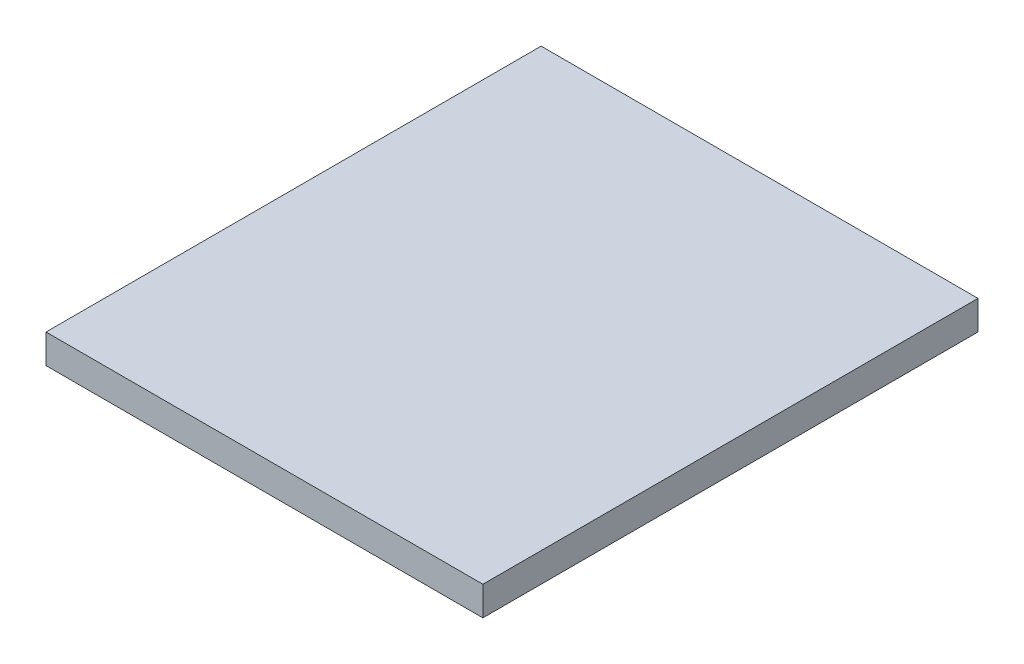
SolidWorks part; units mm, degrees
ref_plane "Alzado" through (0, 0, 0) normal (0, 0, 1) x (1, 0, 0)
ref_plane "Planta" through (0, 0, 0) normal (0, 1, 0) x (1, 0, 0)
ref_plane "Vista lateral" through (0, 0, 0) normal (1, 0, 0) x (0, 0, -1)
sketch "Croquis1" plane through (0, 0, 0) normal (0, 0, 1) x (1, 0, 0)
  line L1 (-40.6456, 29.2089) -> (259.3544, 29.2089)
  line L2 (-40.6456, 29.2089) -> (-40.6456, 9.2089)
  line L3 (-40.6456, 9.2089) -> (259.3544, 9.2089)
  line L4 (259.3544, 29.2089) -> (259.3544, 9.2089)
  dimension "D1" = 300
  dimension "D2" = 20
extrude "Saliente-Extruir1" add sketch "Croquis1" along normal blind 340
